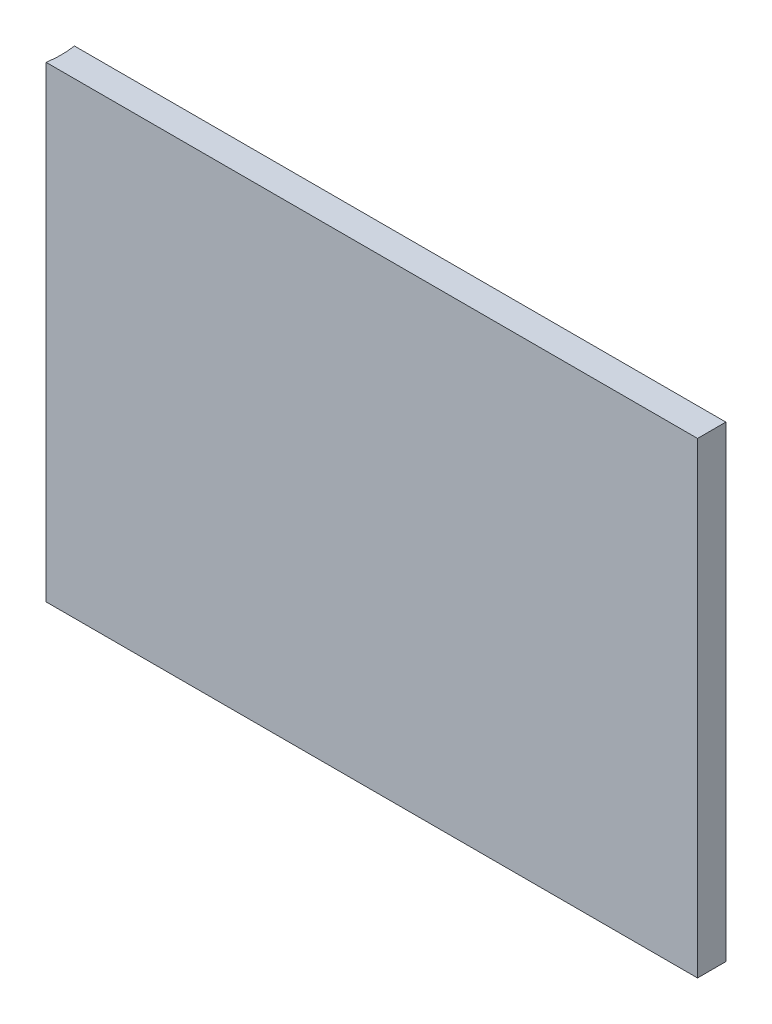
SolidWorks part; units mm, degrees
ref_plane "Front Plane" through (0, 0, 0) normal (0, 0, 1) x (1, 0, 0)
ref_plane "Top Plane" through (0, 0, 0) normal (0, 1, 0) x (1, 0, 0)
ref_plane "Right Plane" through (0, 0, 0) normal (1, 0, 0) x (0, 0, -1)
sketch "Sketch1" plane through (0, 0, 0) normal (0, 0, 1) x (1, 0, 0)
  line L1 (-75.8735, 56.998) -> (70.1765, 56.998)
  line L2 (-75.8735, 56.998) -> (-75.8735, -47.777)
  line L3 (-75.8735, -47.777) -> (70.1765, -47.777)
  line L4 (70.1765, 56.998) -> (70.1765, -47.777)
  dimension "D1" = 146.05
  dimension "D2" = 104.775
extrude "Boss-Extrude1" add sketch "Sketch1" along normal blind 6.35
sketch "Sketch2" plane through (0, 56.998, 0) normal (0, 1, 0) x (1, 0, 0)
  line L4 (-75.8735, 0) -> (-75.8735, -6.35)
  arc A0 (-75.8735, -6.35) -> (-75.8735, 0) centre (-96.3296, -3.175) ccw
  arc A1 (-75.8735, -6.35) -> (-75.8735, 0) centre (-96.3296, -3.175) ccw
  line M4 (-75.8735, 0) -> (-75.8735, -6.35)
  dimension "D1" = 41.402
extrude "Cut-Extrude1" cut sketch "Sketch2" against normal through all contours A0 M4
